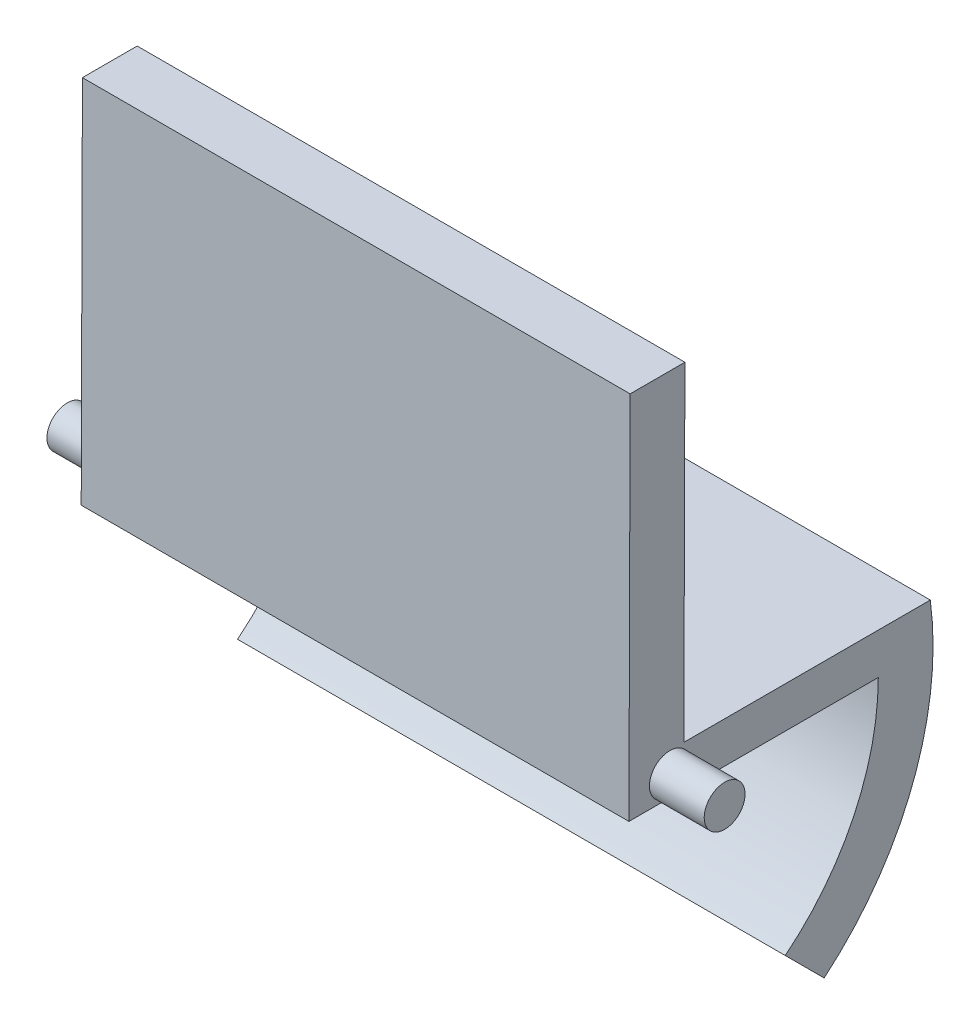
SolidWorks part; units mm, degrees
ref_plane "Plan de face" through (0, 0, 0) normal (0, 0, 1) x (1, 0, 0)
ref_plane "Plan de dessus" through (0, 0, 0) normal (0, 1, 0) x (1, 0, 0)
ref_plane "Plan de droite" through (0, 0, 0) normal (1, 0, 0) x (0, 0, -1)
sketch "Esquisse1" plane through (0, 0, 0) normal (1, 0, 0) x (0, 0, -1)
  line L0 (11.9162, -42.9312) -> (19.0211, -50.0361)
  line L1 (-6.5992, 0.0382) -> (38.4008, 0.0382)
  line L2 (-16.6238, -7.4593) -> (28.9041, -7.4593)
  line L4 (38.4008, 0.0382) -> (38.4008, 0)
  line L5 (-16.6238, -7.4593) -> (-16.4027, 60.0382)
  line L6 (-16.4027, 60.0382) -> (-6.4026, 60.0382)
  line L9 (-6.4026, 60.0382) -> (-6.5992, 0.0382)
  arc A0 (38.4008, 0) -> (19.0211, -50.0361) centre (-16.6238, -7.4593) cw
  arc A1 (28.9041, -7.4593) -> (11.9162, -42.9312) centre (-16.6238, -7.4593) cw
  dimension "D3" = 10
  dimension "D2" = 45
  dimension "D4" = 60
  dimension "D5" = 10
extrude "Boss.-Extru.1" add sketch "Esquisse1" along normal blind 100
sketch "Esquisse3" plane through (0, 0, 0) normal (-1, 0, 0) x (0, 0, 1)
  line L1 (16.6238, -7.4593) -> (-28.9041, -7.4593) construction
  line L2 (16.4027, 60.0382) -> (16.6238, -7.4593) construction
  circle A0 centre (9.1515, -3.7293) radius 3.73
  dimension "D1" = 3.73
  dimension "D2" = 7.46
extrude "Boss.-Extru.2" add sketch "Esquisse3" along normal blind 10 and the other way blind 110
